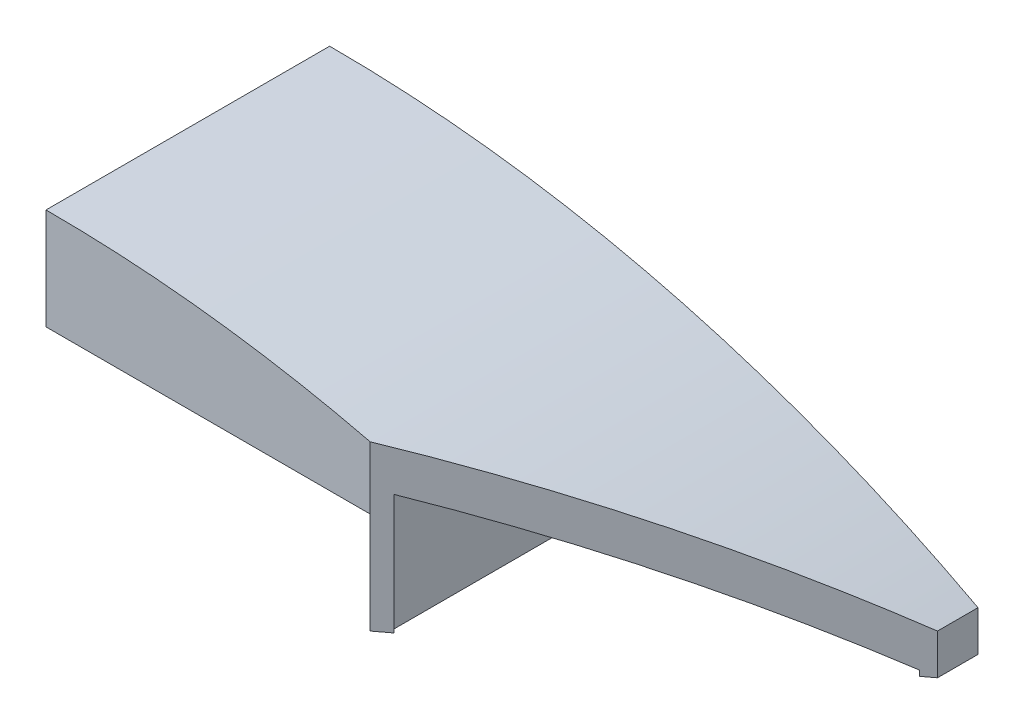
SolidWorks part; units mm, degrees
material "ABS"
ref_plane "Front Plane" through (0, 0, 0) normal (0, 0, 1) x (1, 0, 0)
ref_plane "Top Plane" through (0, 0, 0) normal (0, 1, 0) x (1, 0, 0)
ref_plane "Right Plane" through (0, 0, 0) normal (1, 0, 0) x (0, 0, -1)
sketch "Sketch1" plane through (0, 0, 0) normal (0, 0, 1) x (1, 0, 0)
  line L0 (-10.16, 0) -> (-10.16, 3.175)
  line L1 (-10.16, 0) -> (0, 0)
  line L2 (0, 0) -> (0, -3.175)
  line L3 (0, -3.175) -> (10.16, -3.175)
  line L4 (10.16, -3.175) -> (10.16, -1.905)
  arc A2 (-10.16, 3.175) -> (10.16, -1.905) centre (-10.16, -40.005) cw
  dimension "D1" = 3.175
  dimension "D2" = 20.32
  dimension "D3" = 10.16
  dimension "D4" = 1.27
extrude "Boss-Extrude1" add sketch "Sketch1" along normal mid plane 8.89
sketch "Sketch2" plane through (0, 0, 0) normal (0, -1, 0) x (1, 0, 0)
  line L0 (0, 4.1275) -> (-9.8425, 4.1275)
  line L1 (0, 4.445) -> (0, -4.445) construction
  line L2 (-9.8425, 4.1275) -> (-9.8425, -4.1275)
  line L3 (-9.8425, -4.1275) -> (0, -4.1275)
  line L4 (-10.16, 4.445) -> (0, 4.445) construction
  line L5 (-10.16, 4.445) -> (-10.16, -4.445) construction
  line L6 (-10.16, -4.445) -> (0, -4.445) construction
  line L7 (0, 4.1275) -> (0, -4.1275)
  dimension "D1" = 0.3175
  dimension "D2" = 0.3175
  dimension "D3" = 0.3175
extrude "Cut-Extrude1" cut sketch "Sketch2" against normal offset from surface (0.6548 mm away) 1.27
sketch "Sketch3" plane through (0, -3.175, 0) normal (0, -1, 0) x (1, 0, 0)
  line L8 (0.3175, -4.1275) -> (9.8425, -4.1275)
  line L9 (9.8425, 4.1275) -> (9.8425, -4.1275)
  line L10 (0.3175, 4.1275) -> (9.8425, 4.1275)
  line L11 (0.3175, 4.1275) -> (0.3175, -4.1275)
extrude "Cut-Extrude3" cut sketch "Sketch3" against normal offset from surface (0.1676 mm away) 1.27
ref_plane "Plane1" through (0, -5.08, 0) normal (0, 1, 0) x (1, 0, 0)
sketch "Sketch4" plane through (0, -5.08, 0) normal (0, 1, 0) x (1, 0, 0)
  line L0 (-10.16, -4.445) -> (0, 4.445) construction
  line L1 (0, -4.445) -> (10.16, 4.445) construction
  circle A0 centre (-5.08, 0) radius 2.54
  circle A3 centre (-5.08, 0) radius 1.905
  dimension "D1" = 5.08
  dimension "D2" = 3.81
extrude "Boss-Extrude2" [suppressed] add sketch "Sketch4" along normal up to next
sketch "Sketch5" plane through (0, 0, 0) normal (0, 0, 1) x (1, 0, 0)
  line L0 (4.8895, -5.08) -> (-4.8895, -5.08) construction
  line L1 (-1.7412, -1.905) -> (-7.9443, -1.905)
  line L2 (-1.7412, -1.905) -> (-1.7412, -5.08)
  line L3 (-1.7412, -5.08) -> (-7.9443, -5.08)
  line L4 (-7.9443, -1.905) -> (-7.9443, -5.08)
  line L5 (-10.16, 0) -> (0, 0) construction
  dimension "D1" = 1.905
extrude "Cut-Extrude4" [suppressed] cut sketch "Sketch5" against normal through all both and the other way through all
sketch "Sketch7" plane through (0, 0, 0) normal (0, 1, 0) x (1, 0, 0)
  line L1 (10.16, -4.445) -> (10.16, 4.445) construction
  line L2 (10.16, 3.175) -> (0, -4.445)
  line L3 (-10.16, -4.445) -> (10.16, -4.445) construction
  line L4 (0, -4.445) -> (10.16, -4.445)
  line L5 (10.16, 3.175) -> (10.16, -4.445)
extrude "Cut-Extrude5" cut sketch "Sketch7" against normal through all both and the other way through all
